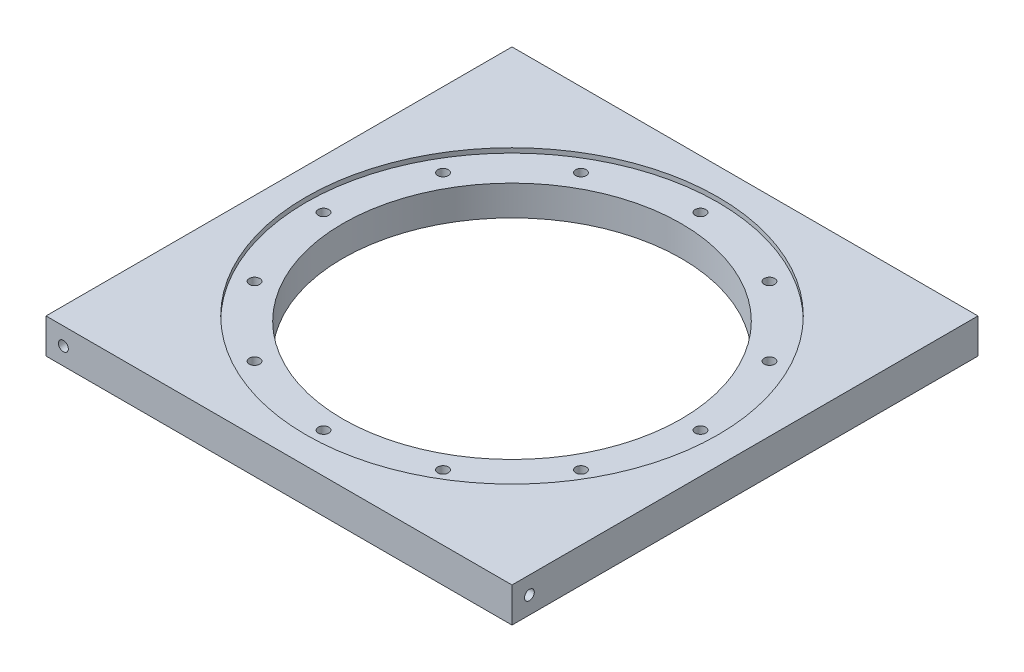
SolidWorks part; units mm, degrees
material "6061-T6 (SS)"
ref_plane "Front Plane" through (0, 0, 0) normal (0, 0, 1) x (1, 0, 0)
ref_plane "Top Plane" through (0, 0, 0) normal (0, 1, 0) x (1, 0, 0)
ref_plane "Right Plane" through (0, 0, 0) normal (1, 0, 0) x (0, 0, -1)
sketch "Sketch1" plane through (0, 0, 0) normal (0, 1, 0) x (1, 0, 0)
  line L5 (0, 0) -> (127.635, 0)
  line L6 (0, 0) -> (0, 127.635)
  line L7 (0, 127.635) -> (127.635, 127.635)
  line L8 (127.635, 0) -> (127.635, 127.635)
  dimension "D1" = 127.635
  dimension "D2" = 127.635
extrude "Boss-Extrude1" add sketch "Sketch1" along normal blind 9.525 contours L5 L8 L7 L6
sketch "Sketch6" plane through (127.635, 0, 0) normal (1, 0, 0) x (0, 0, -1)
  circle A0 centre (4.7625, 4.7625) radius 1.3526
  dimension "D1" = 2.7051
extrude "6-32 hole1" cut sketch "Sketch6" against normal blind 12.7
sketch "Sketch7" plane through (0, 0, -127.635) normal (0, 0, -1) x (-1, 0, 0)
  circle A0 centre (-122.8725, 4.7625) radius 1.3525
  dimension "D1" = 2.7051
extrude "6-32 hole2" cut sketch "Sketch7" against normal blind 12.7
sketch "Sketch8" plane through (0, 0, 0) normal (-1, 0, 0) x (0, 0, 1)
  circle A0 centre (-122.8725, 4.7625) radius 1.3525
  dimension "D1" = 2.7051
extrude "6-32 hole3" cut sketch "Sketch8" against normal blind 12.7
sketch "Sketch9" plane through (0, 0, 0) normal (0, 0, 1) x (1, 0, 0)
  circle A0 centre (4.7625, 4.7625) radius 1.3526
  dimension "D1" = 2.7051
extrude "6-32 hole4" cut sketch "Sketch9" against normal blind 12.7
sketch "Sketch5" plane through (0, 9.525, 0) normal (0, 1, 0) x (1, 0, 0)
  line L0 (63.8175, 0) -> (63.8175, 127.635) construction
  line L3 (0, 0) -> (127.635, 0) construction
  line L8 (0, 127.635) -> (127.635, 127.635) construction
  circle A0 centre (63.8175, 63.8175) radius 46.355
  dimension "D1" = 92.71
extrude "Cut-Extrude1" cut sketch "Sketch5" against normal blind 9.525 contours L0 A0 | A0 L0
sketch "Sketch11" plane through (0, 9.525, 0) normal (0, 1, 0) x (1, 0, 0)
  line L0 (63.8175, 63.8175) -> (63.8175, 115.443) construction
  circle A0 centre (63.8175, 115.443) radius 1.4351
  dimension "D2" = 2.8702
  dimension "D1" = 51.6255
extrude "Cut-Extrude3" cut sketch "Sketch11" against normal through all contours A0
pattern_circular "CirPattern1" count 12 over 360 about axis through (63.8175, 0, -63.8175) along (0, 1, 0) of "Cut-Extrude3"
sketch "Sketch12" plane through (0, 9.525, 0) normal (0, 1, 0) x (1, 0, 0)
  circle A0 centre (63.8175, 63.8175) radius 56.4198
  dimension "D1" = 112.8395
extrude "Cut-Extrude4" cut sketch "Sketch12" against normal blind 1.27
